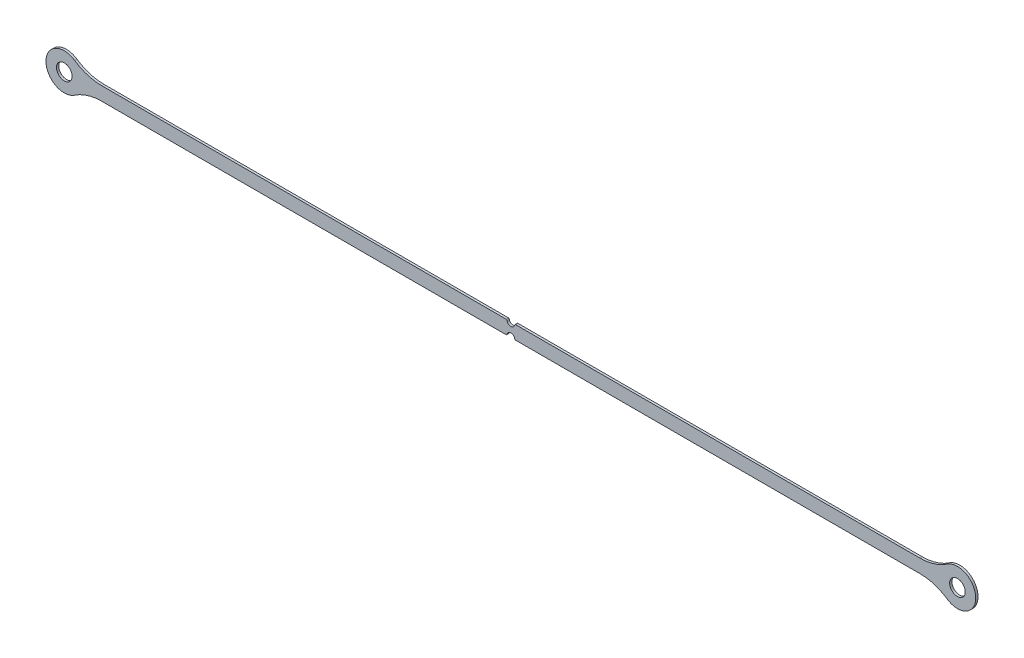
SolidWorks part; units mm, degrees
ref_plane "Front Plane" through (0, 0, 0) normal (0, 0, 1) x (1, 0, 0)
ref_plane "Top Plane" through (0, 0, 0) normal (0, 1, 0) x (1, 0, 0)
ref_plane "Right Plane" through (0, 0, 0) normal (1, 0, 0) x (0, 0, -1)
sketch "Sketch1" plane through (0, 0, 0) normal (0, 0, 1) x (1, 0, 0)
  line L0 (0, -0.5623) -> (0, -10.0623) construction
  line L7 (0, 1.35) -> (0, -1.35)
  line L10 (232, 0) -> (-232, 0) construction
  line L11 (2.5005, 3.5) -> (212.5578, 3.5)
  line L12 (2.5005, -3.5) -> (212.5578, -3.5)
  line L13 (-2.5005, -3.5) -> (-212.5578, -3.5)
  line L14 (-2.5005, 3.5) -> (-212.5578, 3.5)
  arc A0 (226.6463, -7.8478) -> (226.6463, 7.8478) centre (232, 0) ccw
  circle A1 centre (232, 0) radius 4.05
  arc A6 (-2.0102, 3.098) -> (2.0102, 3.098) centre (0, 3.5) ccw
  arc A7 (-2.0102, -3.098) -> (2.0102, -3.098) centre (0, -3.5) cw
  arc A8 (226.6463, 7.8478) -> (212.5578, 3.5) centre (212.5578, 28.5) cw
  arc A9 (226.6463, -7.8478) -> (212.5578, -3.5) centre (212.5578, -28.5) ccw
  arc A10 (2.5005, 3.5) -> (2.0102, 3.098) centre (2.5005, 3) ccw
  arc A11 (2.5005, -3.5) -> (2.0102, -3.098) centre (2.5005, -3) cw
  arc A12 (-2.5005, -3.5) -> (-2.0102, -3.098) centre (-2.5005, -3) ccw
  arc A13 (-2.5005, 3.5) -> (-2.0102, 3.098) centre (-2.5005, 3) cw
  arc A14 (-226.6463, -7.8478) -> (-212.5578, -3.5) centre (-212.5578, -28.5) cw
  arc A15 (-226.6463, 7.8478) -> (-212.5578, 3.5) centre (-212.5578, 28.5) ccw
  circle A16 centre (-232, 0) radius 4.05
  arc A17 (-226.6463, -7.8478) -> (-226.6463, 7.8478) centre (-232, 0) cw
  point P0 (0, 0)
  point P19 (223.1682, 3.5)
  point P22 (223.1682, -3.5)
  point P25 (2.05, 3.5)
  point P28 (2.05, -3.5)
  point P30 (0, 0)
  point P43 (-2.05, -3.5)
  point P44 (-2.05, 3.5)
  point P45 (-223.1682, -3.5)
  point P46 (-223.1682, 3.5)
  dimension "D3" = 2.9
  dimension "D2" = 9.5
  dimension "D4" = 8.1
  dimension "D5" = 3.5
  dimension "D6" = 7
  dimension "D7" = 25
  dimension "D8" = 25
  dimension "D9" = 0.5
  dimension "D10" = 0.5
  dimension "D1" = 232
extrude "Boss-Extrude1" add sketch "Sketch1" along normal blind 1.2
